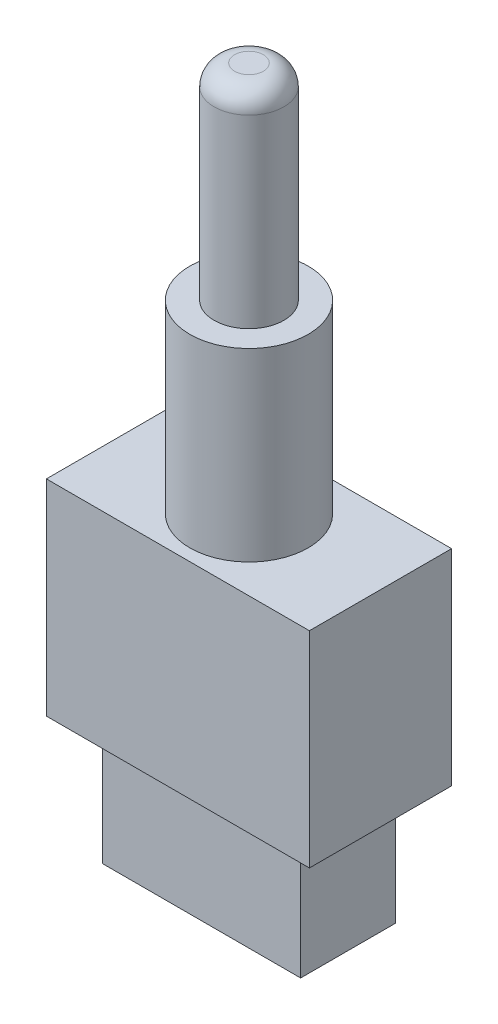
SolidWorks part; units mm, degrees
ref_plane "Front Plane" through (0, 0, 0) normal (0, 0, 1) x (1, 0, 0)
ref_plane "Top Plane" through (0, 0, 0) normal (0, 1, 0) x (1, 0, 0)
ref_plane "Right Plane" through (0, 0, 0) normal (1, 0, 0) x (0, 0, -1)
sketch "Sketch1" plane through (0, 0, 0) normal (0, 1, 0) x (1, 0, 0)
  line L1 (-6.4, 3.46) -> (6.4, 3.46)
  line L2 (-6.4, 3.46) -> (-6.4, -3.46)
  line L3 (-6.4, -3.46) -> (6.4, -3.46)
  line L4 (6.4, 3.46) -> (6.4, -3.46)
  point P4 (6.4, 0)
  point P6 (0, -3.46)
  point P7 (0, 3.46)
  dimension "D1" = 6.92
  dimension "D2" = 12.8
extrude "Boss-Extrude1" add sketch "Sketch1" along normal blind 10
sketch "Sketch2" plane through (0, 10, 0) normal (0, 1, 0) x (1, 0, 0)
  circle A0 centre (0, 0) radius 2.88
  dimension "D1" = 5.76
extrude "Boss-Extrude2" add sketch "Sketch2" along normal blind 9
sketch "Sketch3" plane through (0, 19, 0) normal (0, 1, 0) x (1, 0, 0)
  circle A0 centre (0, 0) radius 1.699
extrude "Boss-Extrude3" add sketch "Sketch3" along normal blind 10
fillet "Fillet1" radius 1 1 edges at (0, 29, 1.699)
sketch "Sketch4" plane through (0, 0, 0) normal (0, -1, 0) x (1, 0, 0)
  line L1 (-4.8243, -2.3109) -> (4.8243, -2.3109)
  line L2 (-4.8243, -2.3109) -> (-4.8243, 2.3109)
  line L3 (-4.8243, 2.3109) -> (4.8243, 2.3109)
  line L4 (4.8243, -2.3109) -> (4.8243, 2.3109)
  point P4 (4.8243, 0)
  point P6 (0, -2.3109)
extrude "Boss-Extrude4" add sketch "Sketch4" along normal blind 6
